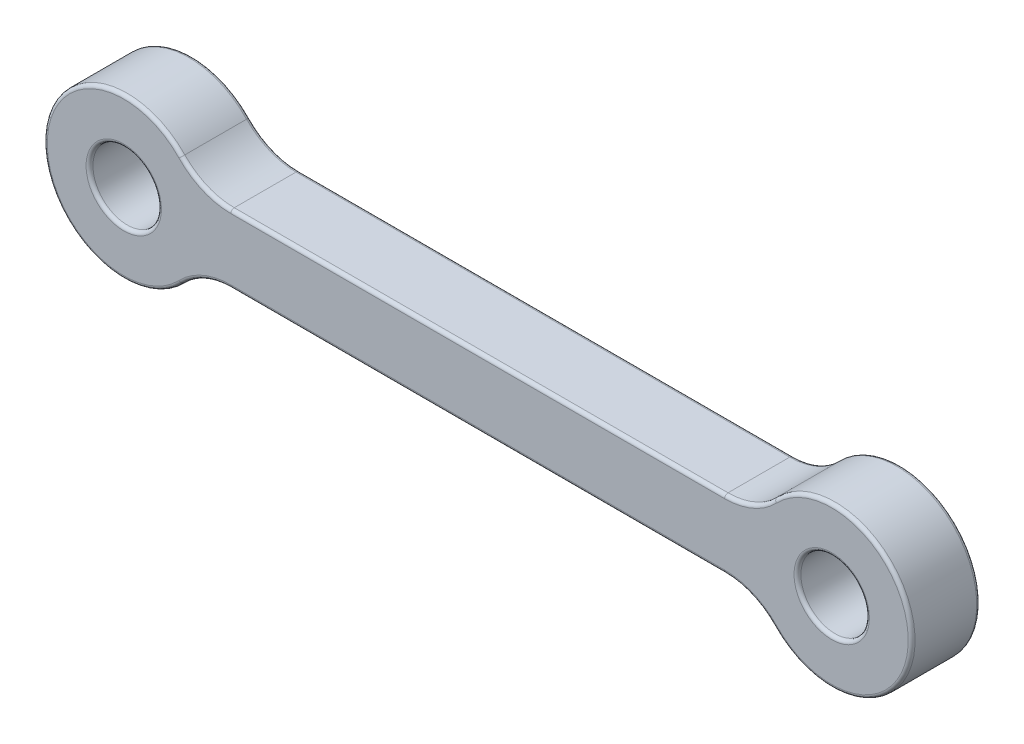
SolidWorks part; units mm, degrees
ref_plane "Front Plane" through (0, 0, 0) normal (0, 0, 1) x (1, 0, 0)
ref_plane "Top Plane" through (0, 0, 0) normal (0, 1, 0) x (1, 0, 0)
ref_plane "Right Plane" through (0, 0, 0) normal (1, 0, 0) x (0, 0, -1)
sketch "Sketch1" plane through (0, 0, 0) normal (0, 0, 1) x (1, 0, 0)
  line L0 (0, 0) -> (31, 0) construction
  line L1 (0, 3.5) -> (31, 3.5) construction
  line L2 (0, -3.5) -> (31, -3.5) construction
  line L3 (15.5, 0) -> (15.5, -3.5) construction
  line L5 (27.8377, -1.5) -> (3.1623, -1.5)
  line L6 (27.8377, -1.5) -> (27.8377, 1.5) construction
  line L7 (27.8377, 1.5) -> (3.1623, 1.5)
  line L8 (3.1623, -1.5) -> (3.1623, 1.5) construction
  line L9 (27.8377, -1.5) -> (3.1623, 1.5) construction
  line L10 (27.8377, 1.5) -> (3.1623, -1.5) construction
  arc A0 (0, 3.5) -> (0, -3.5) centre (0, 0) ccw construction
  arc A1 (31, -3.5) -> (31, 3.5) centre (31, 0) ccw construction
  circle A2 centre (0, 0) radius 1.5
  circle A3 centre (0, 0) radius 3.5
  circle A4 centre (31, 0) radius 1.5
  circle A5 centre (31, 0) radius 3.5
  point P3 (15.5, 0)
  dimension "D3" = 3
  dimension "D1" = 31
  dimension "D2" = 7
  dimension "D4" = 3
extrude "Boss-Extrude1" add sketch "Sketch1" along normal mid plane 3 contours A3 A2 | L5 A5 L7 A3 | A5 A4
fillet "Fillet1" radius 3 4 edges at (3.1623, -1.5, 0) (27.8377, -1.5, 0) (3.1623, 1.5, 0) (27.8377, 1.5, 0)
fillet "Fillet2" radius 0.15 20 edges at (32.5, 0, 1.5) (27.4863, 1.7404, 1.5) (34.5, 0, 1.5) (27.4863, -1.7404, 1.5) (15.5, -1.5, 1.5) (3.5137, -1.7404, 1.5) (-3.5, 0, 1.5) (3.5137, 1.7404, 1.5) (15.5, 1.5, 1.5) (1.5, 0, 1.5) (32.5, 0, -1.5) (3.5137, -1.7404, -1.5) (15.5, -1.5, -1.5) (27.4863, -1.7404, -1.5) (34.5, 0, -1.5) (27.4863, 1.7404, -1.5) (15.5, 1.5, -1.5) (3.5137, 1.7404, -1.5) (-3.5, 0, -1.5) (1.5, 0, -1.5)
